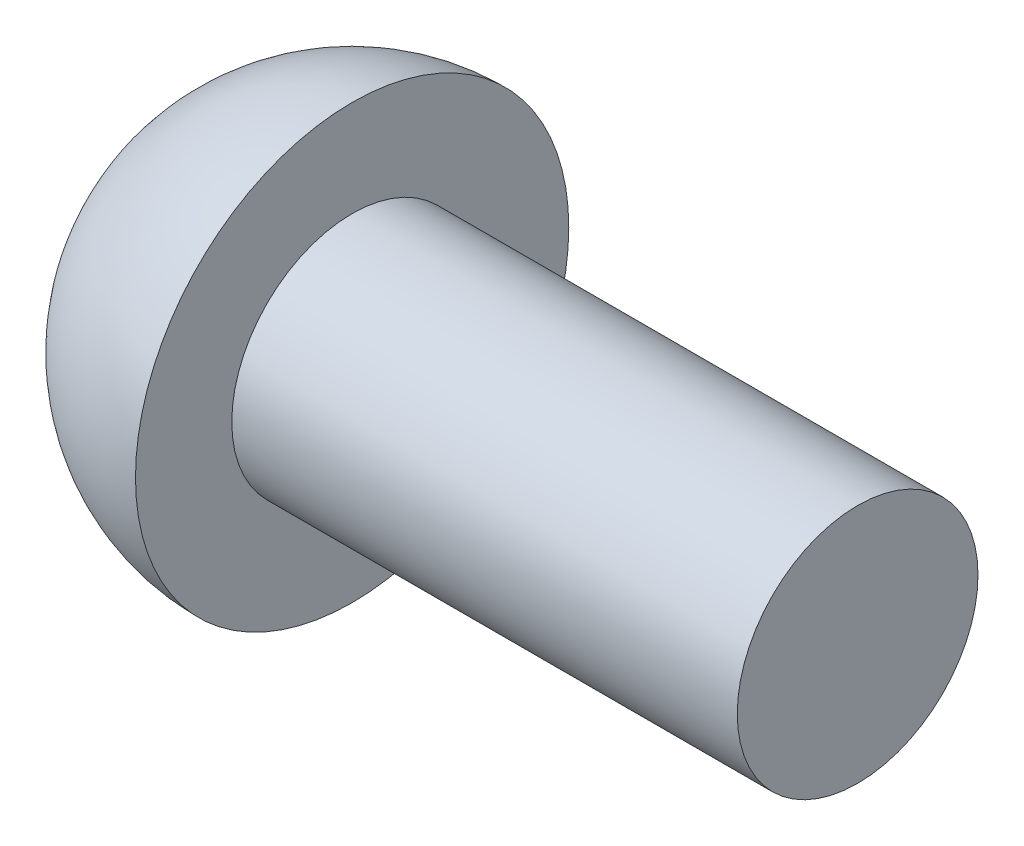
SolidWorks part; units mm, degrees
ref_plane "前基準面" through (0, 0, 0) normal (0, 0, 1) x (1, 0, 0)
ref_plane "上基準面" through (0, 0, 0) normal (0, 1, 0) x (1, 0, 0)
ref_plane "右基準面" through (0, 0, 0) normal (1, 0, 0) x (0, 0, -1)
sketch "草圖1" plane through (0, 0, 0) normal (0, 1, 0) x (1, 0, 0)
  line L0 (0, 0) -> (21, 0)
  line L1 (21, 0) -> (21, 5)
  line L2 (21, 5) -> (0, 5)
  line L3 (0, 5) -> (0, 9)
  line L5 (0, 0) -> (-9, 0)
  arc A1 (0, 9) -> (-9, 0) centre (0, 0) ccw
  dimension "D1" = 9
  dimension "D2" = 21
  dimension "D3" = 5
revolve "旋轉1" add sketch "草圖1" angle 360 about L0
